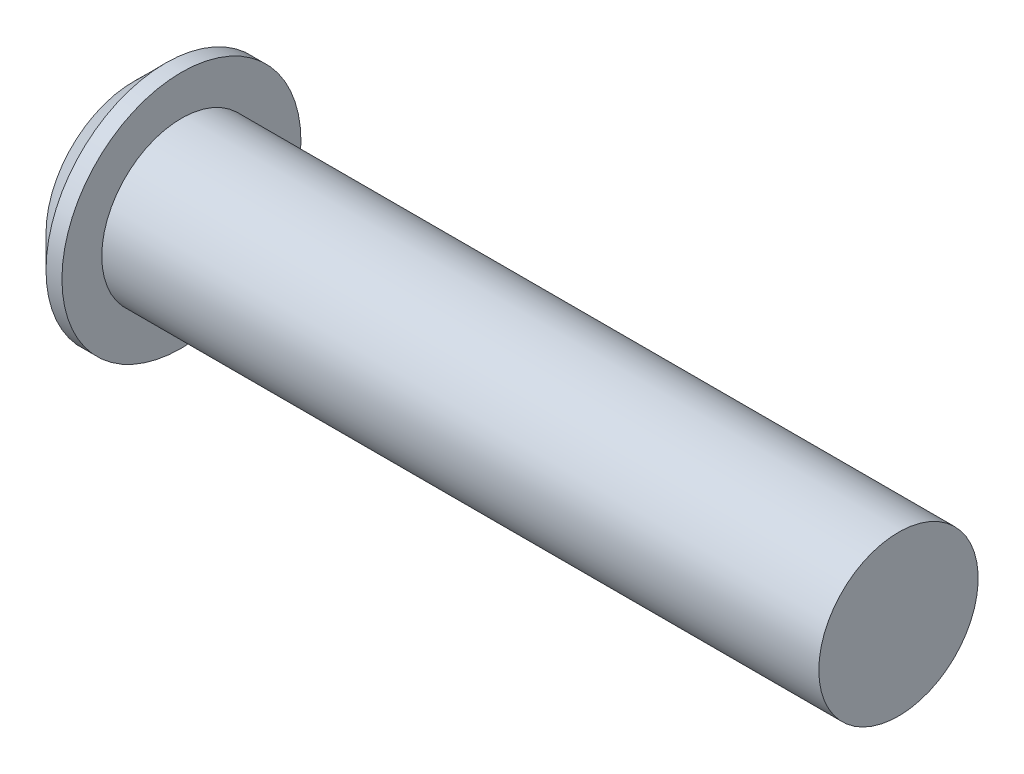
SolidWorks part; units mm, degrees
ref_plane "Ön Düzlem" through (0, 0, 0) normal (0, 0, 1) x (1, 0, 0)
ref_plane "Üst Düzlem" through (0, 0, 0) normal (0, 1, 0) x (1, 0, 0)
ref_plane "Sağ Düzlem" through (0, 0, 0) normal (1, 0, 0) x (0, 0, -1)
sketch "Çizim1" plane through (0, 0, 0) normal (0, 0, 1) x (1, 0, 0)
  line L1 (0, 0) -> (3, 0)
  line L2 (0, 0) -> (0, 7.5)
  line L3 (0, 7.5) -> (3, 7.5)
  line L4 (3, 0) -> (3, 7.5)
  line L5 (3, 0) -> (48, 0)
  line L6 (3, 0) -> (3, 5)
  line L7 (3, 5) -> (48, 5)
  line L8 (48, 0) -> (48, 5)
  dimension "D1" = 5
  dimension "D2" = 3
  dimension "D3" = 7.5
  dimension "D4" = 45
revolve "Döndür1" add sketch "Çizim1" angle 360 about L5
chamfer "Pah1" distance 2 angle 45 1 edges at (0, 0, 7.5)
